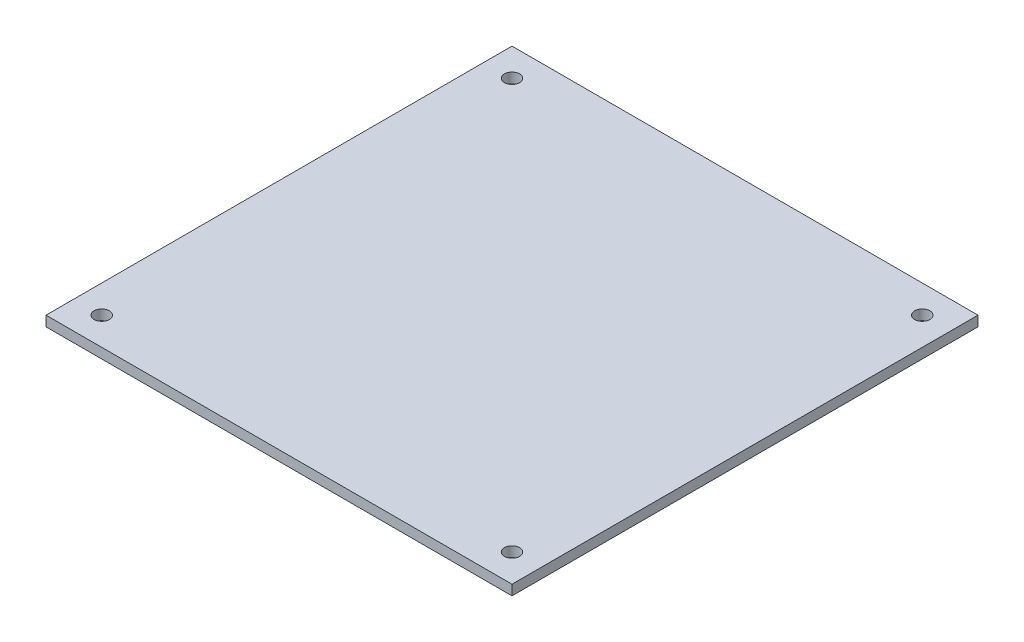
SolidWorks part; units mm, degrees
ref_plane "Front Plane" through (0, 0, 0) normal (0, 0, 1) x (1, 0, 0)
ref_plane "Top Plane" through (0, 0, 0) normal (0, 1, 0) x (1, 0, 0)
ref_plane "Right Plane" through (0, 0, 0) normal (1, 0, 0) x (0, 0, -1)
sketch "Sketch1" plane through (0, 0, 0) normal (0, 1, 0) x (1, 0, 0)
  line L0 (46.0872, 46.195) -> (-45.9128, 46.195)
  line L1 (46.0872, 37.195) -> (46.0872, 46.195)
  line L6 (-45.9128, 46.195) -> (-45.9128, -45.805)
  line L7 (-36.9128, 46.195) -> (-45.9128, 46.195)
  line L8 (-45.9128, -45.805) -> (46.0872, -45.805)
  line L9 (-45.9128, -36.805) -> (-45.9128, -45.805)
  line L12 (46.0872, -45.805) -> (46.0872, 46.195)
  line L13 (37.0872, -45.805) -> (46.0872, -45.805)
  circle A4 centre (40.5872, 40.695) radius 1.5
  circle A5 centre (40.5872, -40.305) radius 1.5
  circle A6 centre (-40.4128, -40.305) radius 1.5
  circle A7 centre (-40.4128, 40.695) radius 1.5
extrude "Boss-Extrude1" add sketch "Sketch1" along normal blind 2 contours L8 L12 L1 L0 L6 A7 A6 A5 A4
